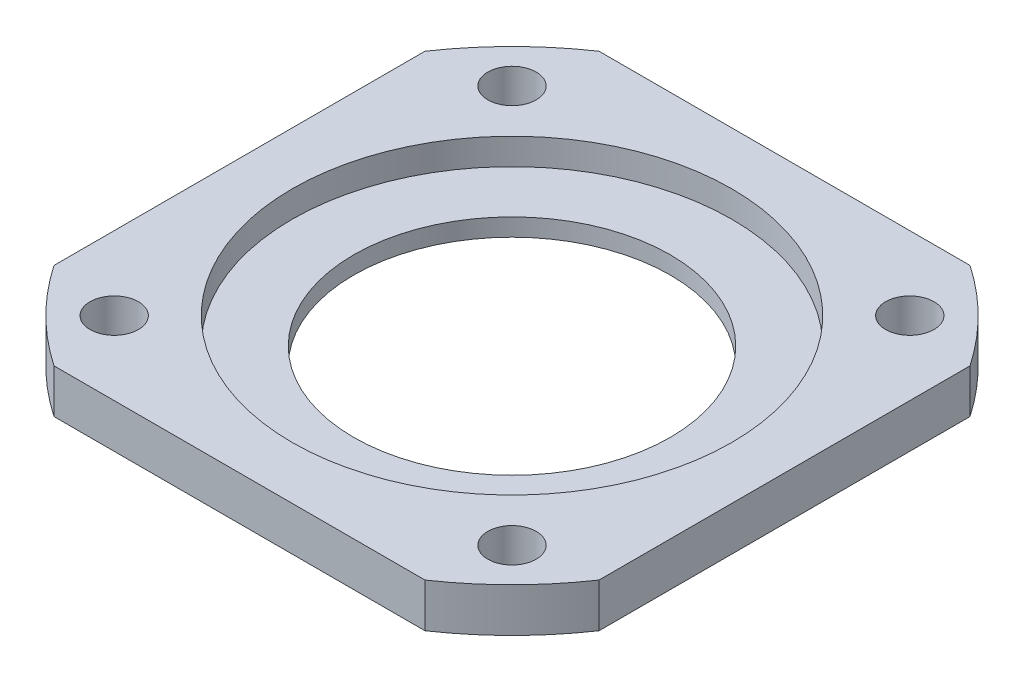
SolidWorks part; units mm, degrees
material "6061-T6 (SS)"
ref_plane "Front Plane" through (0, 0, 0) normal (0, 0, 1) x (1, 0, 0)
ref_plane "Top Plane" through (0, 0, 0) normal (0, 1, 0) x (1, 0, 0)
ref_plane "Right Plane" through (0, 0, 0) normal (1, 0, 0) x (0, 0, -1)
sketch "Sketch1" plane through (0, 0, 0) normal (0, 1, 0) x (1, 0, 0)
  circle A0 centre (0, 0) radius 37.5
  circle A1 centre (0, 0) radius 18
  dimension "D1" = 75
  dimension "D2" = 36
extrude "Boss-Extrude1" add sketch "Sketch1" along normal blind 5
sketch "Sketch2" plane through (0, 5, 0) normal (0, 1, 0) x (1, 0, 0)
  circle A0 centre (0, 0) radius 25
  dimension "D1" = 50
extrude "Cut-Extrude1" cut sketch "Sketch2" against normal blind 3
sketch "Sketch3" plane through (0, 5, 0) normal (0, 1, 0) x (1, 0, 0)
  line L1 (-31, 31) -> (31, 31)
  line L2 (-31, 31) -> (-31, -31)
  line L3 (-31, -31) -> (31, -31)
  line L4 (31, 31) -> (31, -31)
  line L5 (-31, 31) -> (31, -31) construction
  line L6 (-31, -31) -> (31, 31) construction
  point P0 (0, 0)
  dimension "D1" = 62
extrude "Cut-Extrude2" cut sketch "Sketch3" against normal through all flip side to cut
sketch "Sketch4" plane through (0, 5, 0) normal (0, 1, 0) x (1, 0, 0)
  line L1 (-22.6274, 22.6274) -> (22.6274, 22.6274) construction
  line L2 (-22.6274, 22.6274) -> (-22.6274, -22.6274) construction
  line L3 (-22.6274, -22.6274) -> (22.6274, -22.6274) construction
  line L4 (22.6274, 22.6274) -> (22.6274, -22.6274) construction
  line L5 (-22.6274, 22.6274) -> (22.6274, -22.6274) construction
  line L6 (-22.6274, -22.6274) -> (22.6274, 22.6274) construction
  circle A0 centre (-22.6274, 22.6274) radius 2.75
  circle A1 centre (22.6274, 22.6274) radius 2.75
  circle A2 centre (22.6274, -22.6274) radius 2.75
  circle A3 centre (-22.6274, -22.6274) radius 2.75
  point P0 (0, 0)
  dimension "D2" = 5.5
  dimension "D1" = 64
extrude "Cut-Extrude3" cut sketch "Sketch4" against normal through all
